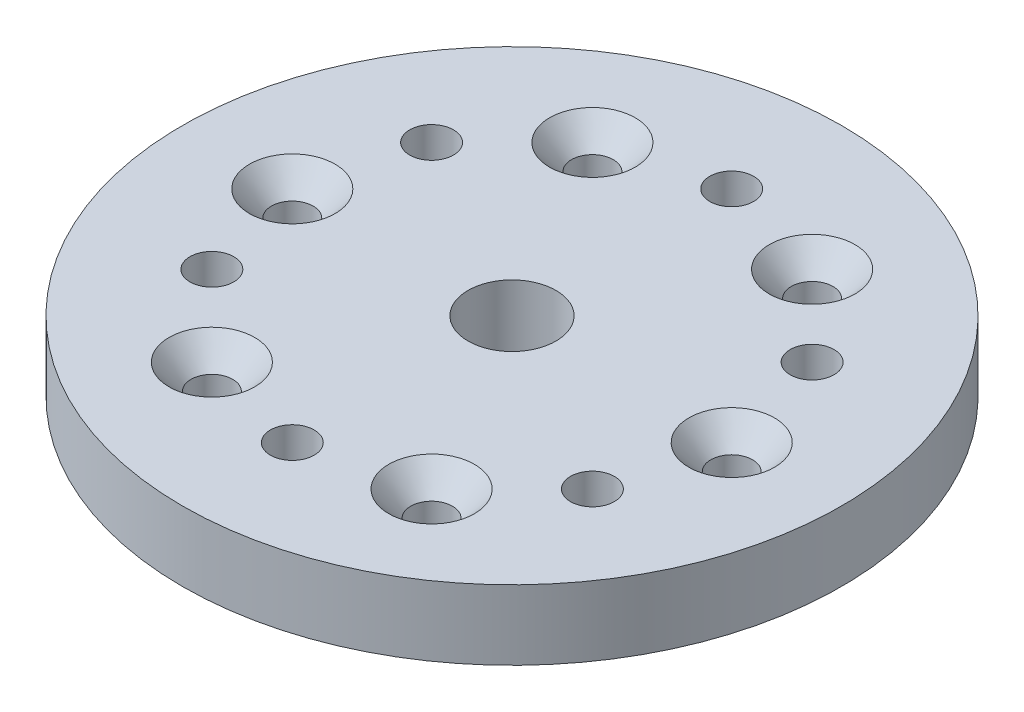
SolidWorks part; units mm, degrees
material "Balsa"
ref_plane "Front" through (0, 0, 0) normal (0, 0, 1) x (1, 0, 0)
ref_plane "Top" through (0, 0, 0) normal (0, 1, 0) x (1, 0, 0)
ref_plane "Right" through (0, 0, 0) normal (1, 0, 0) x (0, 0, -1)
sketch "Sketch1" plane through (0, 0, 0) normal (0, 1, 0) x (1, 0, 0)
  line L0 (0, 0) -> (20, 0) construction
  line L1 (10, 17.3205) -> (0, 0) construction
  line L2 (0, 0) -> (-10, 17.3205) construction
  line L3 (0, 0) -> (0, 20) construction
  line L4 (0, 0) -> (-17.3205, 10) construction
  line L5 (0, 0) -> (-17.3205, -10) construction
  circle A0 centre (0, 0) radius 30
  circle A1 centre (20, 0) radius 1.8986
  circle A2 centre (10, -17.3205) radius 1.8986
  circle A3 centre (-10, -17.3205) radius 1.8986
  circle A4 centre (-20, 0) radius 1.8986
  circle A5 centre (-10, 17.3205) radius 1.8986
  circle A6 centre (10, 17.3205) radius 1.8986
  circle A7 centre (0, 20) radius 1.9939
  circle A8 centre (17.3205, 10) radius 1.9939
  circle A9 centre (17.3205, -10) radius 1.9939
  circle A10 centre (0, -20) radius 1.9939
  circle A11 centre (-17.3205, -10) radius 1.9939
  circle A12 centre (-17.3205, 10) radius 1.9939
  circle A13 centre (0, 0) radius 4
  dimension "D1" = 60
  dimension "D2" = 3.7973
  dimension "D5" = 3.9878
  dimension "D7" = 8
  dimension "D3" = 20
  dimension "D4" = 6
  dimension "D6" = 6
extrude "Boss-Extrude1" add sketch "Sketch1" along normal blind 6.35
other "Move Face1" [suppressed] parameters "D1"=0.08
chamfer "Chamfer1" distance 2.301 angle 41 6 edges at (-10, 6.35, -15.4219) (-20, 6.35, 1.8986) (-10, 6.35, 19.2192) (10, 6.35, 19.2192) (20, 6.35, 1.8986) (10, 6.35, -15.4219)
